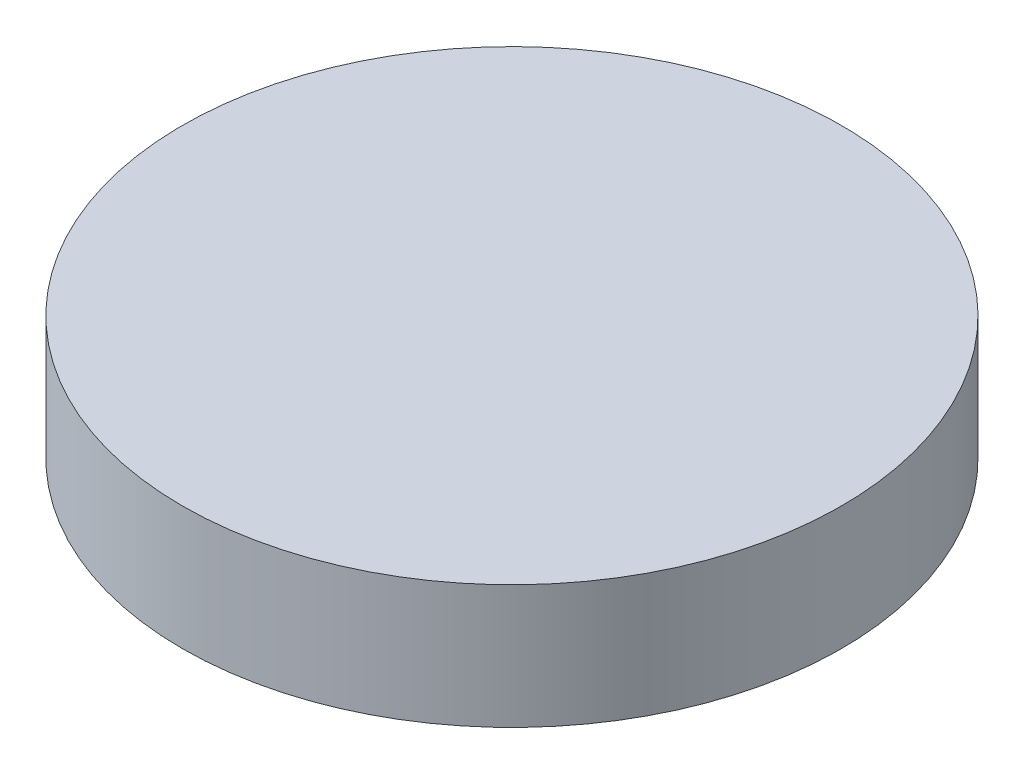
SolidWorks part; units mm, degrees
material "Lasercut ABS"
ref_plane "Front Plane" through (0, 0, 0) normal (0, 0, 1) x (1, 0, 0)
ref_plane "Top Plane" through (0, 0, 0) normal (0, 1, 0) x (1, 0, 0)
ref_plane "Right Plane" through (0, 0, 0) normal (1, 0, 0) x (0, 0, -1)
sketch "Sketch1" plane through (0, 0, 0) normal (0, 1, 0) x (1, 0, 0)
  circle A0 centre (0, 0) radius 8
  dimension "D1" = 16
extrude "Boss-Extrude1" add sketch "Sketch1" along normal blind 3
